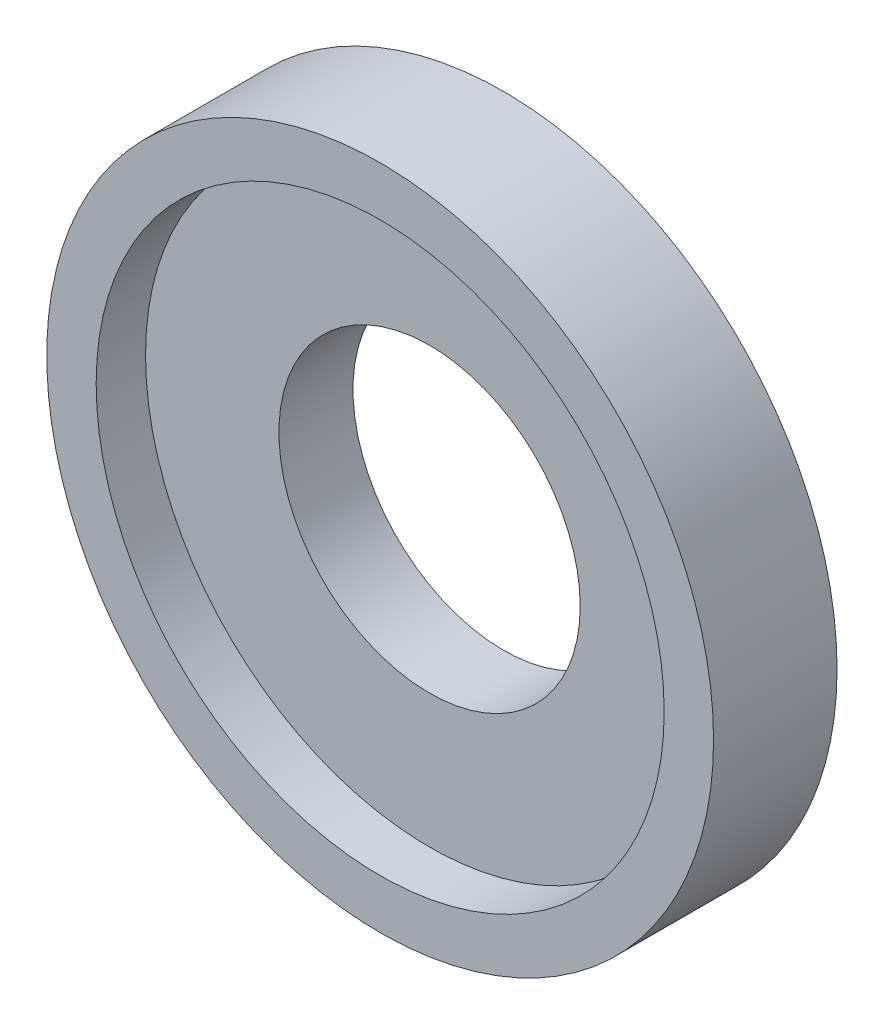
SolidWorks part; units mm, degrees
ref_plane "前视基准面" through (0, 0, 0) normal (0, 0, 1) x (1, 0, 0)
ref_plane "上视基准面" through (0, 0, 0) normal (0, 1, 0) x (1, 0, 0)
ref_plane "右视基准面" through (0, 0, 0) normal (1, 0, 0) x (0, 0, -1)
sketch "草图1" plane through (0, 0, 0) normal (0, 0, 1) x (1, 0, 0)
  circle A0 centre (0, 0) radius 6.75
  dimension "D1" = 13.5
extrude "凸台-拉伸1" add sketch "草图1" along normal blind 2.5
sketch "草图2" plane through (0, 0, 2.5) normal (0, 0, 1) x (1, 0, 0)
  circle A0 centre (0, 0) radius 3.05
  dimension "D1" = 6.1
extrude "切除-拉伸1" cut sketch "草图2" against normal through all
sketch "草图3" plane through (0, 0, 2.5) normal (0, 0, 1) x (1, 0, 0)
  circle A0 centre (0, 0) radius 5.75
  dimension "D1" = 11.5
extrude "切除-拉伸2" cut sketch "草图3" against normal blind 1
